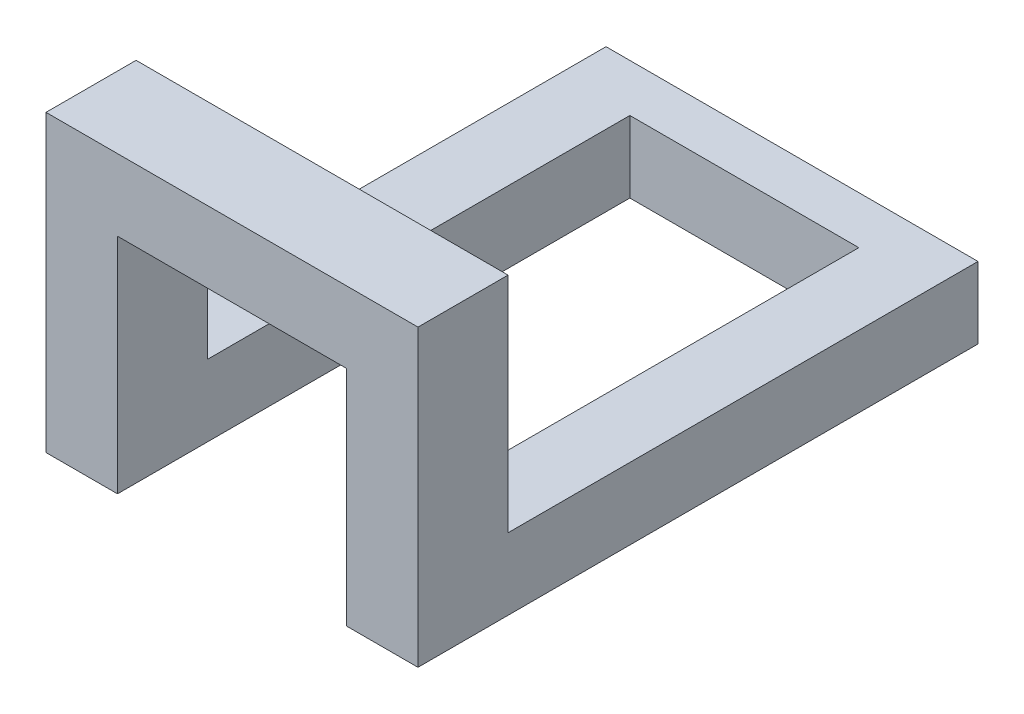
SolidWorks part; units mm, degrees
ref_plane "Front Plane" through (0, 0, 0) normal (0, 0, 1) x (1, 0, 0)
ref_plane "Top Plane" through (0, 0, 0) normal (0, 1, 0) x (1, 0, 0)
ref_plane "Right Plane" through (0, 0, 0) normal (1, 0, 0) x (0, 0, -1)
sketch "Sketch1" plane through (0, 0, 0) normal (0, 1, 0) x (1, 0, 0)
  line L12 (44.2903, 10.1471) -> (44.2903, 14.9471)
  line L13 (44.2903, 10.1471) -> (24.4703, 10.1471)
  line L16 (24.4703, 10.1471) -> (24.4703, 14.9471)
  line L17 (24.4703, 14.9471) -> (44.2903, 14.9471)
  line L18 (39.6303, 14.9471) -> (35.9423, 14.9471) construction
  line L19 (34.9303, 10.1471) -> (39.6303, 10.1471) construction
  line L20 (40.4803, 10.9971) -> (40.4803, 15.7971) construction
  line L21 (28.2803, 15.7971) -> (28.2803, 10.9971) construction
  dimension "D1" = 3.81
  dimension "D2" = 3.81
extrude "Boss-Extrude1" add sketch "Sketch1" along normal blind 3.81 contours L17 L12 L13 L16
sketch "Sketch2" plane through (0, 0, 0) normal (0, -1, 0) x (1, 0, 0)
  line L0 (24.4703, -14.9471) -> (44.2903, -14.9471) construction
  line L1 (24.4703, -10.1471) -> (28.2803, -10.1471)
  line L2 (24.4703, -10.1471) -> (24.4703, -14.9471)
  line L3 (24.4703, -14.9471) -> (28.2803, -14.9471)
  line L4 (28.2803, -10.1471) -> (28.2803, -14.9471)
  line L5 (44.2903, -10.1471) -> (24.4703, -10.1471) construction
  line L6 (44.2903, -14.9471) -> (40.4803, -14.9471)
  line L7 (44.2903, -14.9471) -> (44.2903, -10.1471)
  line L8 (44.2903, -10.1471) -> (40.4803, -10.1471)
  line L9 (40.4803, -14.9471) -> (40.4803, -10.1471)
  dimension "D1" = 3.81
  dimension "D2" = 3.81
extrude "Boss-Extrude2" add sketch "Sketch2" along normal up to surface (11.89 mm away)
sketch "Sketch3" plane through (0, 0, -14.9471) normal (0, 0, -1) x (-1, 0, 0)
  line L0 (-40.4803, -11.89) -> (-40.4803, 0) construction
  line L1 (-44.2903, -11.89) -> (-40.4803, -11.89)
  line L2 (-44.2903, -11.89) -> (-44.2903, -8.08)
  line L3 (-44.2903, -8.08) -> (-40.4803, -8.08)
  line L4 (-40.4803, -11.89) -> (-40.4803, -8.08)
  line L11 (-24.4703, 3.81) -> (-24.4703, -11.89) construction
  line L12 (-28.2803, -11.89) -> (-24.4703, -11.89)
  line L13 (-28.2803, -11.89) -> (-28.2803, -8.08)
  line L14 (-28.2803, -8.08) -> (-24.4703, -8.08)
  line L15 (-24.4703, -11.89) -> (-24.4703, -8.08)
  dimension "D1" = 3.81
  dimension "D2" = 3.81
extrude "Boss-Extrude3" add sketch "Sketch3" along normal up to surface (22.5 mm away)
sketch "Sketch4" plane through (0, 0, -37.4471) normal (0, 0, -1) x (-1, 0, 0)
  line L1 (-44.2903, -8.08) -> (-24.4703, -8.08)
  line L2 (-44.2903, -8.08) -> (-44.2903, -11.89)
  line L3 (-44.2903, -11.89) -> (-24.4703, -11.89)
  line L4 (-24.4703, -8.08) -> (-24.4703, -11.89)
extrude "Boss-Extrude4" add sketch "Sketch4" along normal blind 2.54
sketch "Sketch5" plane through (0, 0, -39.9871) normal (0, 0, -1) x (-1, 0, 0)
  line L0 (-36.891, -10.1413) -> (-30.0352, -8.5021)
